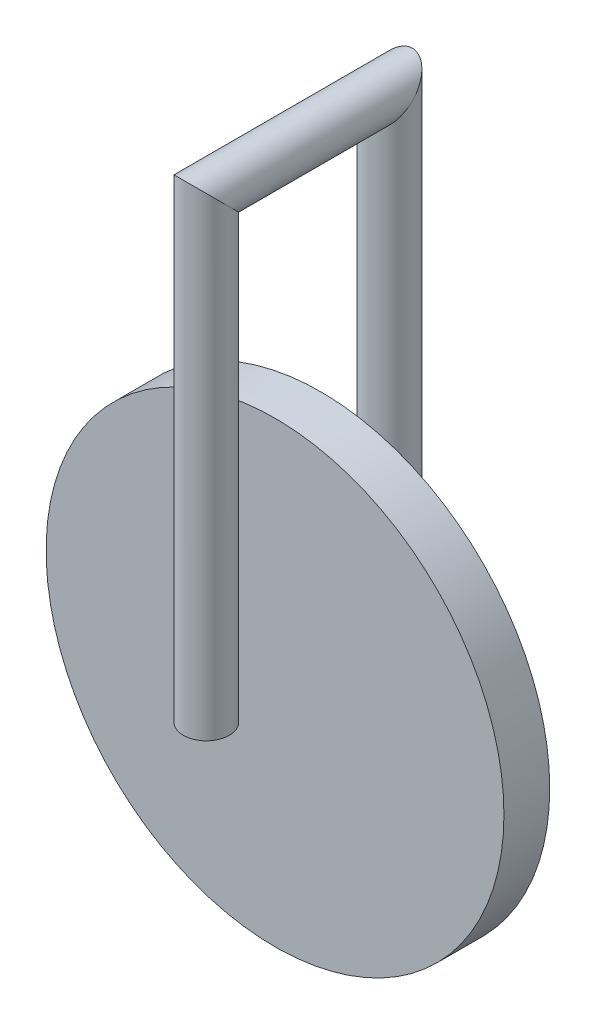
SolidWorks part; units mm, degrees
ref_plane "Front Plane" through (0, 0, 0) normal (0, 0, 1) x (1, 0, 0)
ref_plane "Top Plane" through (0, 0, 0) normal (0, 1, 0) x (1, 0, 0)
ref_plane "Right Plane" through (0, 0, 0) normal (1, 0, 0) x (0, 0, -1)
sketch "Sketch1" plane through (0, 0, 0) normal (0, 0, 1) x (1, 0, 0)
  circle A0 centre (0, 0) radius 50
  dimension "D1" = 100
extrude "Boss-Extrude1" add sketch "Sketch1" along normal mid plane 10
sketch "Sketch3" plane through (0, 0, 0) normal (0, 1, 0) x (1, 0, 0)
  line L0 (0, 0) -> (0, -20)
  line L1 (0, -20) -> (0, 20)
  dimension "D1" = 20
  dimension "D2" = 20
sketch "Sketch5" plane through (0, 0, 0) normal (1, 0, 0) x (0, 0, -1)
  line L0 (-20, 0) -> (-20, 100)
  line L1 (-20, 0) -> (20, 0) construction
  line L2 (-20, 100) -> (20, 100)
  line L3 (20, 100) -> (20, 0)
  line L4 (0, 100) -> (0, 150)
  line L5 (-20, 0) -> (20, 0)
  dimension "D1" = 100
  dimension "D2" = 50
sweep "Sweep1" add path "Sketch5" circular profile diameter 10 parameters "D3"=10
